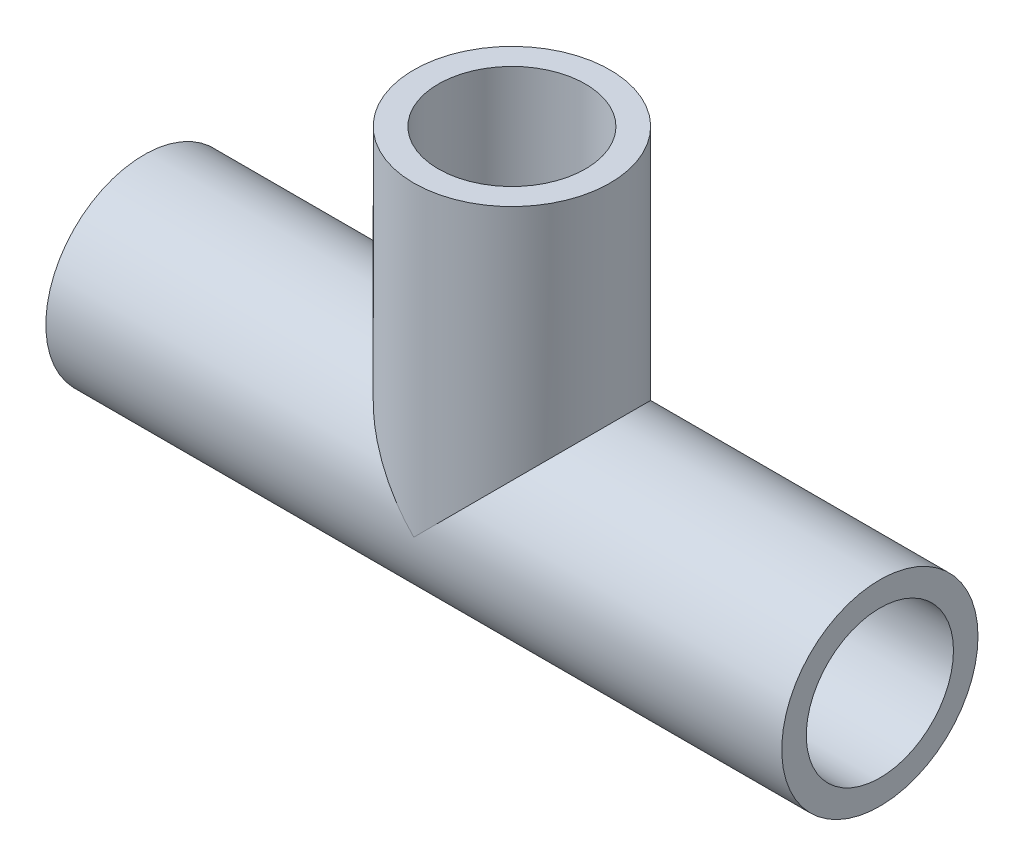
SolidWorks part; units mm, degrees
ref_plane "Front Plane" through (0, 0, 0) normal (0, 0, 1) x (1, 0, 0)
ref_plane "Top Plane" through (0, 0, 0) normal (0, 1, 0) x (1, 0, 0)
ref_plane "Right Plane" through (0, 0, 0) normal (1, 0, 0) x (0, 0, -1)
sketch "Sketch1" plane through (0, 0, 0) normal (1, 0, 0) x (0, 0, -1)
  circle A0 centre (0, 0) radius 6
  circle A1 centre (0, 0) radius 8
  dimension "D1" = 12
  dimension "D2" = 16
extrude "Boss-Extrude1" add sketch "Sketch1" along normal mid plane 60
ref_plane "Plane1" through (0, 25, 0) normal (0, 1, 0) x (1, 0, 0)
sketch "Sketch3" plane through (0, 25, 0) normal (0, 1, 0) x (1, 0, 0)
  circle A0 centre (0, 0) radius 8
  dimension "D1" = 16
extrude "Boss-Extrude2" add sketch "Sketch3" against normal up to surface (25 mm away) up to face at (30, 0, -8)
sketch "Sketch4" plane through (0, 25, 0) normal (0, 1, 0) x (1, 0, 0)
  circle A0 centre (0, 0) radius 6
  dimension "D1" = 12
extrude "Cut-Extrude1" cut sketch "Sketch4" against normal blind 25
